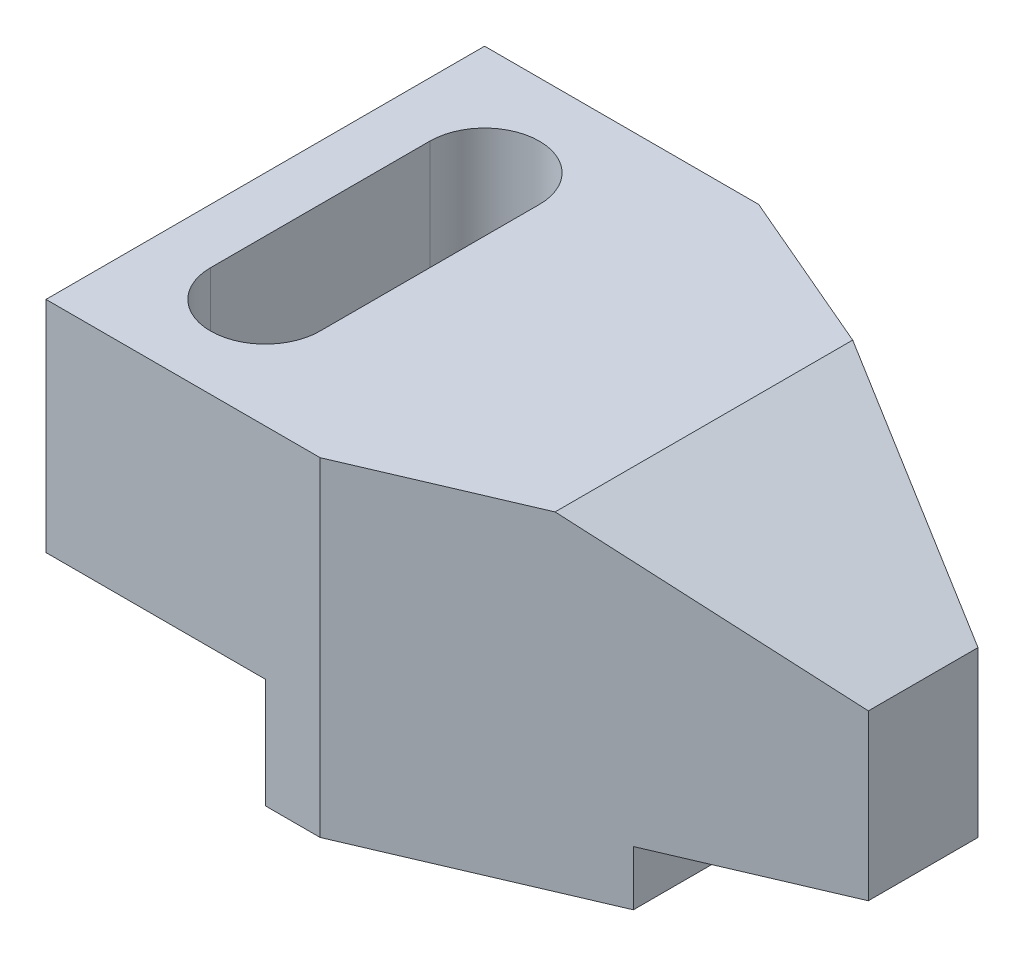
SolidWorks part; units mm, degrees
ref_plane "Front Plane" through (0, 0, 0) normal (0, 0, 1) x (1, 0, 0)
ref_plane "Top Plane" through (0, 0, 0) normal (0, 1, 0) x (1, 0, 0)
ref_plane "Right Plane" through (0, 0, 0) normal (1, 0, 0) x (0, 0, -1)
sketch "Sketch1" plane through (0, 0, 0) normal (0, 1, 0) x (1, 0, 0)
  line L0 (20, 40) -> (30, 40)
  line L1 (20, -40) -> (-20, -40)
  line L2 (20, -40) -> (20, 40)
  line L3 (20, 40) -> (-20, 40)
  line L4 (-20, -40) -> (-20, 40)
  line L5 (20, -40) -> (-20, 40) construction
  line L6 (20, 40) -> (-20, -40) construction
  line L7 (30, 40) -> (30, -40)
  line L8 (30, -40) -> (20, -40)
  line L9 (30, 40) -> (100, 10)
  line L12 (100, 10) -> (100, -10)
  line L13 (100, -10) -> (30, -40)
  point P0 (0, 0)
  dimension "D1" = 40
  dimension "D2" = 80
  dimension "D5" = 10
  dimension "D6" = 20
extrude "Boss-Extrude1" add sketch "Sketch1" along normal blind 60 contours L4 L1 L2 L3 | L13 L12 L9 L7 | L8 L7 L0 L2
sketch "Sketch2" plane through (0, 0, 40) normal (0, 0, 1) x (1, 0, 0)
  line L0 (30, 0) -> (-20, 0) construction
  line L1 (-20, 0) -> (20, 0)
  line L2 (-20, 0) -> (-20, 20)
  line L3 (-20, 20) -> (20, 20)
  line L4 (20, 0) -> (20, 20)
  line L5 (-20, 60) -> (-20, 0) construction
  dimension "D1" = 40
  dimension "D2" = 20
extrude "Cut-Extrude1" cut sketch "Sketch2" against normal through all
sketch "Sketch3" plane through (0, 0, 0) normal (0, -1, 0) x (1, 0, 0)
  line L0 (100, 0) -> (70, 0)
  line L1 (100, -10) -> (100, 10) construction
  line L2 (70, 22.8571) -> (70, -22.8571)
  line L3 (100, 10) -> (30, 40) construction
  line L4 (30, -40) -> (100, -10) construction
  line L5 (70, -22.8571) -> (70, 22.8571)
  line L6 (100, 10) -> (70, 22.8571)
  line L7 (100, 10) -> (100, -10)
  line L8 (100, -10) -> (70, -22.8571)
  line M5 (30, -40) -> (100, -10)
  line M6 (100, -10) -> (100, 10)
  line M7 (100, 10) -> (30, 40)
  dimension "D1" = 30
extrude "Cut-Extrude2" cut sketch "Sketch3" against normal blind 10 contours L2 L0 M7 M6 | L0 L2 M5 M6
sketch "Sketch5" plane through (0, 60, 0) normal (0, 1, 0) x (1, 0, 0)
  line L0 (0, -20) -> (0, 20) construction
  line L1 (-10, -20) -> (-10, 20)
  line L2 (10, -20) -> (10, 20)
  line L3 (30, -40) -> (-20, -40) construction
  line L4 (30, 40) -> (-20, 40) construction
  line L5 (-20, -40) -> (-20, 40) construction
  arc A0 (-10, -20) -> (10, -20) centre (0, -20) ccw
  arc A1 (10, 20) -> (-10, 20) centre (0, 20) ccw
  point P3 (0, 0)
  point P8 (0, -30)
  point P11 (0, 30)
  dimension "D1" = 10
  dimension "D2" = 10
  dimension "D3" = 10
  dimension "D4" = 10
extrude "Cut-Extrude3" cut sketch "Sketch5" against normal through all
sketch "Sketch6" plane through (0, 0, 40) normal (0, 0, 1) x (1, 0, 0)
  line L0 (60, 60) -> (100, 60)
  line L1 (100, 60) -> (30, 60) construction
  line L2 (60, 60) -> (100, 40)
  line L3 (100, 60) -> (100, 10) construction
  line L4 (100, 40) -> (100, 60)
  dimension "D1" = 40
  dimension "D2" = 20
extrude "Cut-Extrude4" cut sketch "Sketch6" against normal through all
